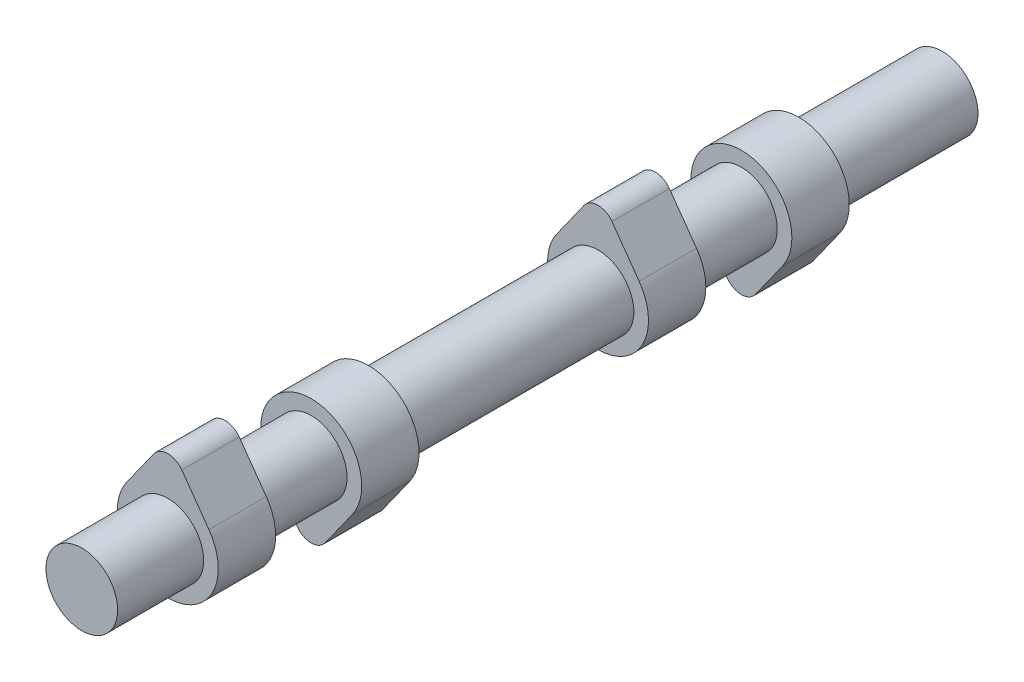
SolidWorks part; units mm, degrees
ref_plane "Front Plane" through (0, 0, 0) normal (0, 0, 1) x (1, 0, 0)
ref_plane "Top Plane" through (0, 0, 0) normal (0, 1, 0) x (1, 0, 0)
ref_plane "Right Plane" through (0, 0, 0) normal (1, 0, 0) x (0, 0, -1)
sketch "Sketch1" plane through (0, 0, 0) normal (0, 0, 1) x (1, 0, 0)
  circle A0 centre (0, 0) radius 6.25
  dimension "D1" = 12.5
extrude "Boss-Extrude1" add sketch "Sketch1" along normal blind 150
ref_plane "Plane1" through (0, 0, 135) normal (0, 0, 1) x (1, 0, 0)
sketch "Sketch2" plane through (0, 0, 135) normal (0, 0, 1) x (1, 0, 0)
  line L0 (-2.4438, 11.74) -> (-7.1686, 5.104)
  line L1 (2.4438, 11.74) -> (7.1686, 5.104)
  arc A0 (-7.1686, 5.104) -> (7.1686, 5.104) centre (0, 0) ccw
  arc A1 (2.4438, 11.74) -> (-2.4438, 11.74) centre (0, 10) ccw
  circle A2 centre (0, 0) radius 6.25
  dimension "D1" = 17.6
  dimension "D3" = 6
  dimension "D2" = 10
extrude "Boss-Extrude2" add sketch "Sketch2" against normal blind 10
ref_plane "Plane2" through (0, 0, 110) normal (0, 0, -1) x (-1, 0, 0)
sketch "Sketch3" plane through (0, 0, 110) normal (0, 0, -1) x (-1, 0, 0)
  line L0 (2.4438, -11.74) -> (7.1686, -5.104)
  line L1 (-2.4438, -11.74) -> (-7.1686, -5.104)
  circle A1 centre (0, 0) radius 6.25
  arc A2 (-2.4438, -11.74) -> (2.4438, -11.74) centre (0, -10) ccw
  arc A4 (7.1686, -5.104) -> (-7.1686, -5.104) centre (0, 0) ccw
  dimension "D2" = 6
  dimension "D1" = 10
extrude "Boss-Extrude3" add sketch "Sketch3" along normal blind 10
ref_plane "Plane3" through (0, 0, 60) normal (0, 0, -1) x (-1, 0, 0)
sketch "Sketch4" plane through (0, 0, 60) normal (0, 0, -1) x (-1, 0, 0)
  line L2 (-2.4438, 11.74) -> (-7.1686, 5.104)
  line L3 (7.1686, 5.104) -> (2.4438, 11.74)
  line L4 (-2.4438, 11.74) -> (-7.1686, 5.104)
  line L5 (7.1686, 5.104) -> (2.4438, 11.74)
  arc A2 (2.4438, 11.74) -> (-2.4438, 11.74) centre (0, 10) ccw
  arc A3 (-7.1686, 5.104) -> (7.1686, 5.104) centre (0, 0) ccw
  arc A4 (2.4438, 11.74) -> (-2.4438, 11.74) centre (0, 10) ccw
  arc A5 (-7.1686, 5.104) -> (7.1686, 5.104) centre (0, 0) ccw
  dimension "D1" = 0
extrude "Boss-Extrude4" add sketch "Sketch4" along normal blind 10
ref_plane "Plane4" through (0, 0, 35) normal (0, 0, -1) x (-1, 0, 0)
sketch "Sketch5" plane through (0, 0, 35) normal (0, 0, -1) x (-1, 0, 0)
  line L2 (2.4438, -11.74) -> (7.1686, -5.104)
  line L3 (-7.1686, -5.104) -> (-2.4438, -11.74)
  line L4 (2.4438, -11.74) -> (7.1686, -5.104)
  line L5 (-7.1686, -5.104) -> (-2.4438, -11.74)
  arc A2 (-2.4438, -11.74) -> (2.4438, -11.74) centre (0, -10) ccw
  arc A3 (7.1686, -5.104) -> (-7.1686, -5.104) centre (0, 0) ccw
  arc A4 (-2.4438, -11.74) -> (2.4438, -11.74) centre (0, -10) ccw
  arc A5 (7.1686, -5.104) -> (-7.1686, -5.104) centre (0, 0) ccw
  dimension "D1" = 0
extrude "Boss-Extrude5" add sketch "Sketch5" along normal blind 10
